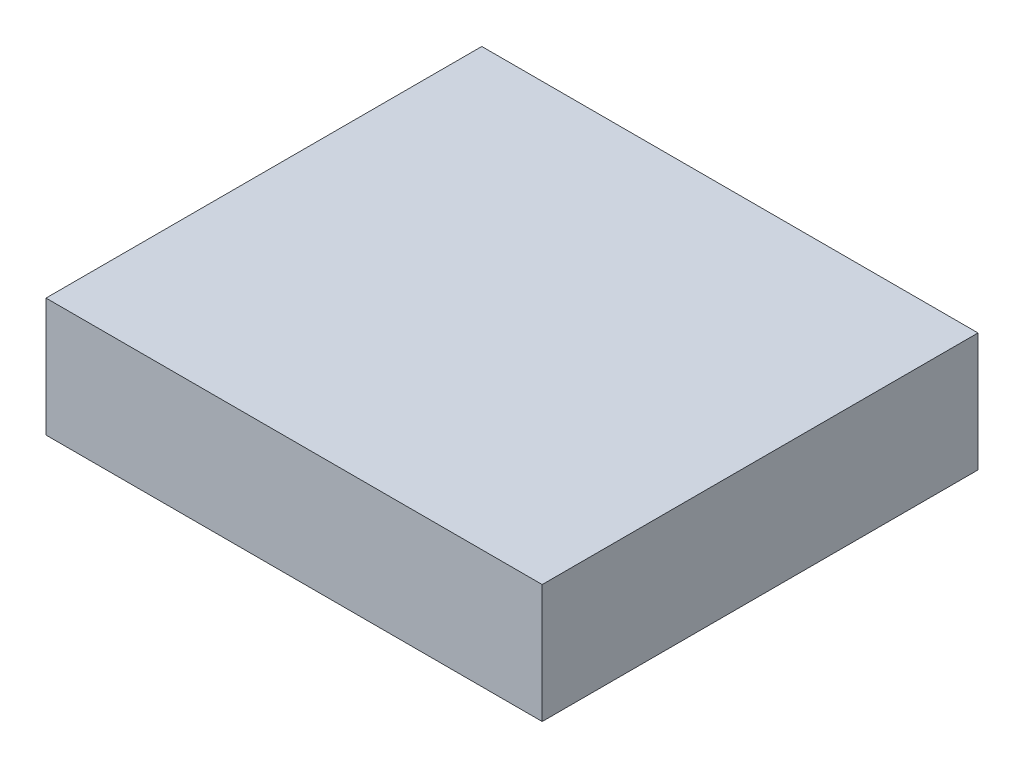
SolidWorks part; units mm, degrees
ref_plane "Front Plane" through (0, 0, 0) normal (0, 0, 1) x (1, 0, 0)
ref_plane "Top Plane" through (0, 0, 0) normal (0, 1, 0) x (1, 0, 0)
ref_plane "Right Plane" through (0, 0, 0) normal (1, 0, 0) x (0, 0, -1)
sketch "Sketch1" plane through (0, 0, 0) normal (0, 1, 0) x (1, 0, 0)
  line L1 (-57.5, -50.5) -> (57.5, -50.5)
  line L2 (-57.5, -50.5) -> (-57.5, 50.5)
  line L3 (-57.5, 50.5) -> (57.5, 50.5)
  line L4 (57.5, -50.5) -> (57.5, 50.5)
  line L5 (-57.5, -50.5) -> (57.5, 50.5) construction
  line L6 (-57.5, 50.5) -> (57.5, -50.5) construction
  point P0 (0, 0)
  dimension "D1" = 101
  dimension "D2" = 115
extrude "Boss-Extrude1" add sketch "Sketch1" along normal blind 27.5
ref_plane "Plane1" through (0, 0, 0) normal (1, 0, 0) x (0, 0, -1)
